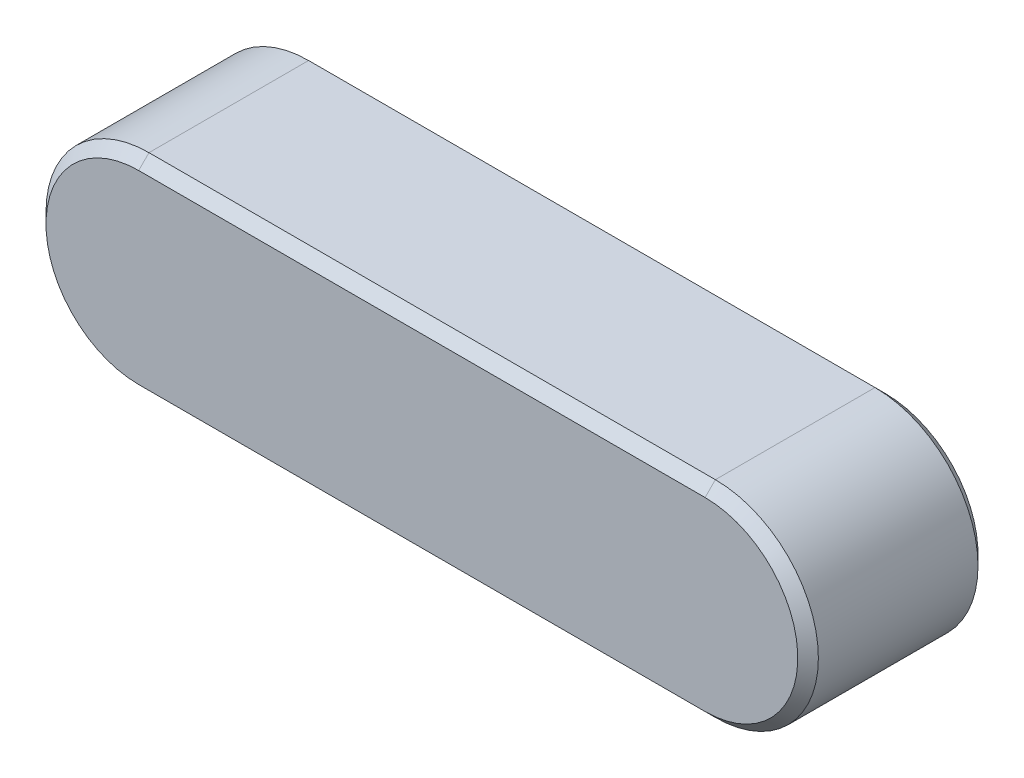
SolidWorks part; units mm, degrees
ref_plane "Front" through (0, 0, 0) normal (0, 0, 1) x (1, 0, 0)
ref_plane "Top" through (0, 0, 0) normal (0, 1, 0) x (1, 0, 0)
ref_plane "Right" through (0, 0, 0) normal (1, 0, 0) x (0, 0, -1)
sketch "Sketch1" plane through (0, 0, 0) normal (0, 0, 1) x (1, 0, 0)
  line L0 (-22, 4) -> (0, 4)
  line L1 (0, -4) -> (-22, -4)
  arc A0 (0, 4) -> (0, -4) centre (0, 0) cw
  arc A1 (-22, -4) -> (-22, 4) centre (-22, 0) cw
  dimension "L" = 30
  dimension "b" = 8
extrude "BaseKey" add sketch "Sketch1" along normal mid plane 7
sketch "Sketch2" plane through (0, 0, 0) normal (0, 0, 1) x (1, 0, 0)
  line L1 (-26, 4) -> (4, 4)
  line L2 (-26, 4) -> (-26, -4)
  line L3 (-26, -4) -> (4, -4)
  line L4 (4, 4) -> (4, -4)
  line L6 (0, -4) -> (-22, -4) construction
  line L7 (-22, 4) -> (0, 4) construction
  arc A2 (0, -4) -> (0, 4) centre (0, 0) ccw construction
  arc A3 (-22, 4) -> (-22, -4) centre (-22, 0) ccw construction
extrude "Extrude1" [suppressed] add sketch "Sketch2" along normal mid plane 7
sketch "Sketch3" plane through (0, 0, 0) normal (0, 0, 1) x (1, 0, 0)
  line L0 (4, 4) -> (-22, 4)
  line L1 (-22, -4) -> (4, -4)
  line L2 (4, -4) -> (4, 4)
  line L5 (-22, 4) -> (0, 4) construction
  arc A0 (-22, 4) -> (-22, -4) centre (-22, 0) ccw
  arc A1 (0, -4) -> (0, 4) centre (0, 0) ccw construction
  arc A4 (-22, 4) -> (-22, -4) centre (-22, 0) ccw construction
extrude "Extrude2" [suppressed] add sketch "Sketch3" along normal mid plane 7
chamfer "Chamfer1" distance 0.4 angle 45 8 edges at (4, 0, -3.5) (-11, -4, -3.5) (-26, 0, -3.5) (-11, 4, -3.5) (-26, 0, 3.5) (-11, -4, 3.5) (4, 0, 3.5) (-11, 4, 3.5)
equation "\"D1@Extrude1\"=\"h@BaseKey\""
equation "\"D1@Extrude2\"=\"h@BaseKey\""
